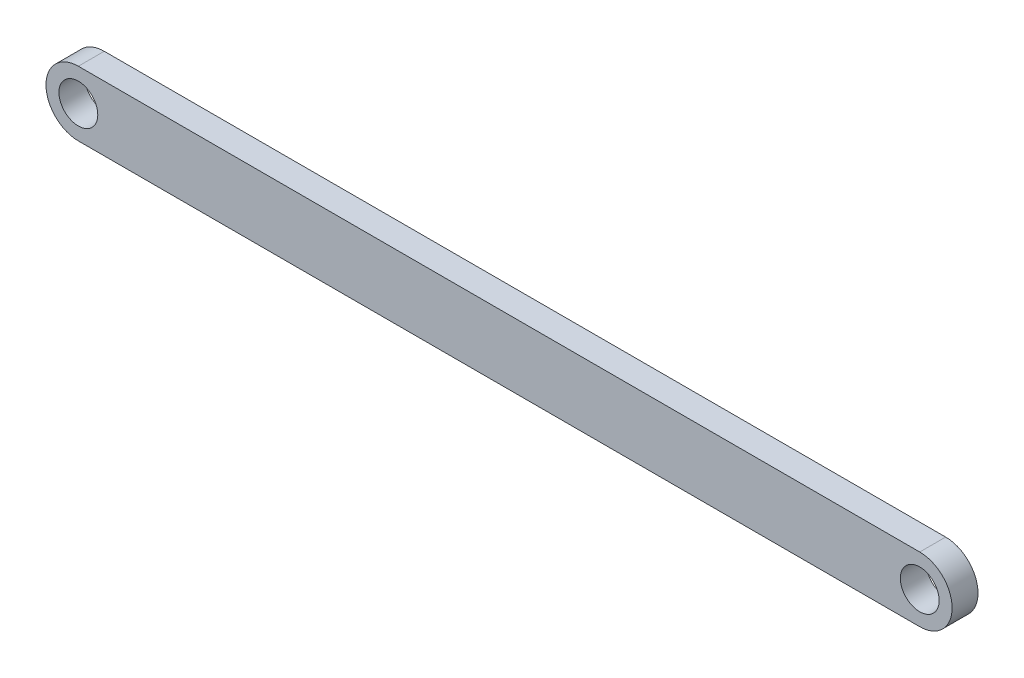
SolidWorks part; units mm, degrees
ref_plane "Front Plane" through (0, 0, 0) normal (0, 0, 1) x (1, 0, 0)
ref_plane "Top Plane" through (0, 0, 0) normal (0, 1, 0) x (1, 0, 0)
ref_plane "Right Plane" through (0, 0, 0) normal (1, 0, 0) x (0, 0, -1)
sketch "Sketch1" plane through (0, 0, 0) normal (0, 0, 1) x (1, 0, 0)
  line L0 (0, 0) -> (-65, 0) construction
  line L1 (0, -2.5) -> (-65, -2.5)
  line L2 (0, 2.5) -> (-65, 2.5)
  arc A0 (0, -2.5) -> (0, 2.5) centre (0, 0) ccw
  arc A1 (-65, 2.5) -> (-65, -2.5) centre (-65, 0) ccw
  circle A2 centre (-65, 0) radius 1.5
  circle A3 centre (0, 0) radius 1.5
  point P3 (-32.5, 0)
  dimension "D2" = 2.5
  dimension "D3" = 3
  dimension "D1" = 65
extrude "Boss-Extrude1" add sketch "Sketch1" along normal blind 2
